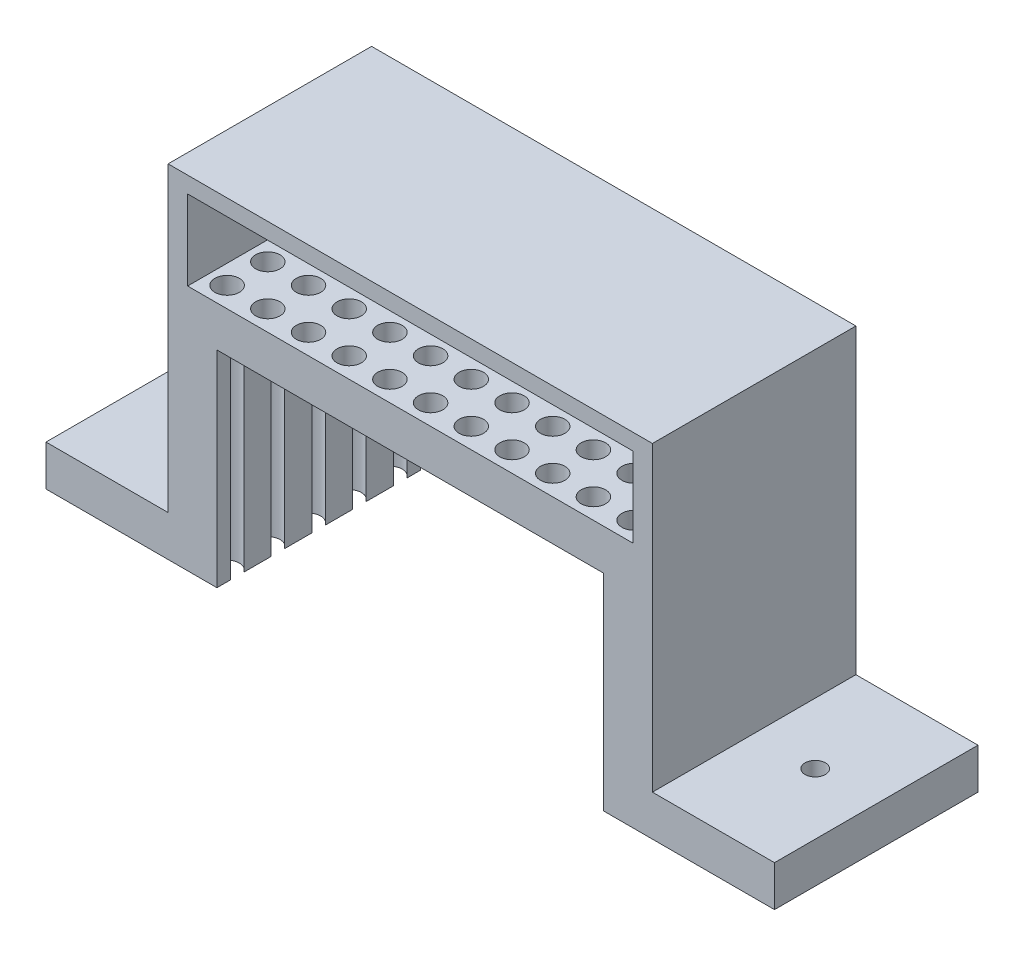
SolidWorks part; units mm, degrees
ref_plane "Front Plane" through (0, 0, 0) normal (0, 0, 1) x (1, 0, 0)
ref_plane "Top Plane" through (0, 0, 0) normal (0, 1, 0) x (1, 0, 0)
ref_plane "Right Plane" through (0, 0, 0) normal (1, 0, 0) x (0, 0, -1)
sketch "Sketch1" plane through (0, 0, 0) normal (0, 0, 1) x (1, 0, 0)
  line L0 (0, 66.096) -> (0, -29.5348) construction
  line L1 (23.75, 18.8856) -> (-23.75, 18.8856)
  line L2 (-23.75, 18.8856) -> (-23.75, -6.4144)
  line L3 (-23.75, -6.4144) -> (-34.9537, -6.4144)
  line L4 (-29.75, -1.4144) -> (-29.75, 35.6856)
  line L5 (-29.75, 35.6856) -> (-22.75, 35.6856)
  line L6 (-22.75, 35.6856) -> (-22.75, 33.6856)
  line L7 (-22.75, 33.6856) -> (-27.35, 33.6856)
  line L8 (-27.35, 33.6856) -> (-27.35, 23.8856)
  line L9 (-27.35, 23.8856) -> (27.35, 23.8856)
  line L10 (27.35, 33.6856) -> (27.35, 23.8856)
  line L11 (22.75, 33.6856) -> (27.35, 33.6856)
  line L12 (22.75, 35.6856) -> (22.75, 33.6856)
  line L13 (29.75, 35.6856) -> (22.75, 35.6856)
  line L14 (29.75, -1.4144) -> (29.75, 35.6856)
  line L15 (23.75, -6.4144) -> (34.9537, -6.4144)
  line L16 (23.75, 18.8856) -> (23.75, -6.4144)
  line L17 (-34.9537, -6.4144) -> (-44.75, -6.4144)
  line L18 (-44.75, -6.4144) -> (-44.75, -1.4144)
  line L19 (-44.75, -1.4144) -> (-29.75, -1.4144)
  line L20 (44.75, -6.4144) -> (44.75, -1.4144)
  line L21 (34.9537, -6.4144) -> (44.75, -6.4144)
  line L22 (44.75, -1.4144) -> (29.75, -1.4144)
  point P15 (0, 23.8856)
  point P16 (0, 18.8856)
  dimension "D1" = 25.3
  dimension "D2" = 47.5
  dimension "D3" = 9.8
  dimension "D4" = 54.7
  dimension "D5" = 5
  dimension "D6" = 6
  dimension "D7" = 15
  dimension "D8" = 5
  dimension "D9" = 2
  dimension "D10" = 7
  dimension "D11" = 34.9537
  dimension "D12" = 18.8856
extrude "Boss-Extrude1" add sketch "Sketch1" along normal blind 25
sketch "Sketch5" plane through (0, -1.4144, 0) normal (0, 1, 0) x (1, 0, 0)
  line L0 (-44.75, 0) -> (-29.75, -25) construction
  line L1 (-29.75, 0) -> (-44.75, -25) construction
  point P10 (-37.25, -12.5)
hole_wizard "M3 Tapped Hole1" positions "Sketch5" profile "Sketch6" tap size "M3" standard "DIN" end condition through all
sketch "Sketch6" plane through (-37.25, -1.4144, 12.5) normal (1, 0, 0) x (0, 0, 1)
  line L0 (0, 0) -> (0, 5)
  line L1 (0, 5) -> (1.25, 5)
  line L2 (1.25, 5) -> (1.25, 0)
  line L5 (1.25, 0) -> (0, 0)
  line L11 (0, -6.35) -> (0, 107.95) construction
  dimension "Thru Tap Drill Dia." = 2.5
  dimension "Thru Tap Drill Depth" = 5
cosmetic thread "Hole Thread1" parameters "D2"=3
sketch "Sketch7" plane through (0, 23.8856, 0) normal (0, 1, 0) x (1, 0, 0)
  line L0 (0, 0) -> (0, -25) construction
  line L1 (27.35, -25) -> (-27.35, -25) construction
  line L2 (29.75, 0) -> (44.75, -25) construction
  line L3 (29.75, -25) -> (44.75, 0) construction
  point P15 (37.25, -12.5)
hole_wizard "M3 Tapped Hole2" positions "Sketch7" profile "Sketch8" tap size "M3" standard "DIN" end condition through all
sketch "Sketch8" plane through (37.25, 23.8856, 12.5) normal (1, 0, 0) x (0, 0, 1)
  line L0 (0, 0) -> (0, 30.3)
  line L1 (0, 30.3) -> (1.25, 30.3)
  line L2 (1.25, 30.3) -> (1.25, 0)
  line L5 (1.25, 0) -> (0, 0)
  line L11 (0, -6.35) -> (0, 107.95) construction
  dimension "Thru Tap Drill Dia." = 2.5
  dimension "Thru Tap Drill Depth" = 30.3
cosmetic thread "Hole Thread2" parameters "D2"=3
sketch "Sketch9" plane through (0, 23.8856, 0) normal (0, 1, 0) x (1, 0, 0)
  line L0 (27.35, 0) -> (-27.35, 0) construction
  line L3 (-27.35, -25) -> (-27.35, 0) construction
  circle A0 centre (0, -12.5) radius 1.5
  dimension "D1" = 12.5
  dimension "D2" = 27.35
extrude "Cut-Extrude1" cut sketch "Sketch9" against normal through all
pattern_linear "LPattern1" count 6 spacing 5 along (1, 0, 0) count 6 spacing 5 along (-1, 0, 0) of "Cut-Extrude1"
pattern_linear "LPattern2" count 3 spacing 5 along (0, 0, -1) count 3 spacing 5 along (0, 0, 1) of "LPattern1", "Cut-Extrude1"
sketch "Sketch13" plane through (0, 35.6856, 0) normal (0, 1, 0) x (1, 0, 0)
  line L1 (-22.75, 0) -> (22.75, 0)
  line L2 (-22.75, 0) -> (-22.75, -25)
  line L3 (-22.75, -25) -> (22.75, -25)
  line L4 (22.75, 0) -> (22.75, -25)
extrude "Boss-Extrude2" add sketch "Sketch13" against normal blind 2
